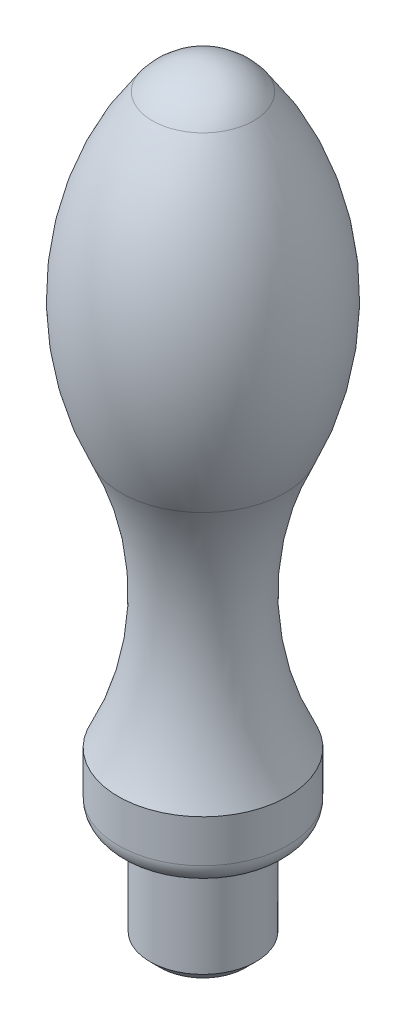
SolidWorks part; units mm, degrees
ref_plane "Front Plane" through (0, 0, 0) normal (0, 0, 1) x (1, 0, 0)
ref_plane "Top Plane" through (0, 0, 0) normal (0, 1, 0) x (1, 0, 0)
ref_plane "Right Plane" through (0, 0, 0) normal (1, 0, 0) x (0, 0, -1)
sketch "Sketch1" plane through (0, 0, 0) normal (0, 0, 1) x (1, 0, 0)
  line L0 (0, -4.5369) -> (0, 73.4733) construction
  line L1 (0, 0) -> (4, 0)
  line L2 (5, 1) -> (5, 10)
  line L3 (5, 10) -> (6, 10)
  line L4 (8, 12) -> (8, 16)
  line L5 (4, 0) -> (5, 1)
  line L6 (0, 0) -> (0, 72)
  arc A0 (8, 12) -> (6, 10) centre (6, 12) cw
  arc A1 (8, 16) -> (7.727, 40.6695) centre (32.9983, 28.6129) cw
  arc A2 (7.727, 40.6695) -> (4.7848, 69.6202) centre (-17.5443, 52.7261) ccw
  arc A3 (4.7848, 69.6202) -> (0, 72) centre (0, 66) ccw
  point P4 (5, 0)
  point P10 (8, 10)
  point P15 (0, 0)
  point P17 (0, 0)
  point P18 (5, 28.3031)
  point P22 (0, 73.4733)
  point P24 (0, 0)
  dimension "D5" = 2
  dimension "D6" = 28
  dimension "D9" = 72
  dimension "D11" = 6
  dimension "D7" = 28
  dimension "D1" = 8
  dimension "D2" = 5
  dimension "D3" = 10
  dimension "D4" = 6
  dimension "D10" = 5
revolve "Revolve1" add sketch "Sketch1" angle 360 about L0
